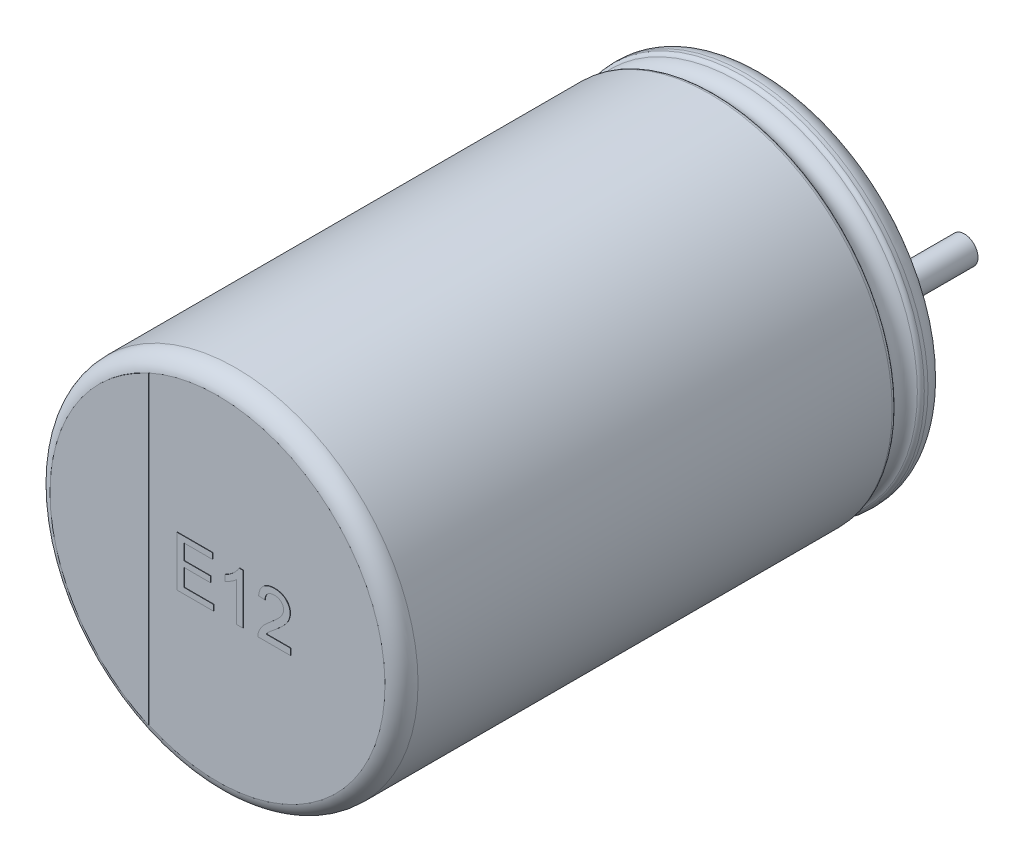
SolidWorks part; units mm, degrees
ref_plane "Plan de face" through (0, 0, 0) normal (0, 0, 1) x (1, 0, 0)
ref_plane "Plan de dessus" through (0, 0, 0) normal (0, 1, 0) x (1, 0, 0)
ref_plane "Plan de droite" through (0, 0, 0) normal (1, 0, 0) x (0, 0, -1)
sketch "Sketch10" plane through (0, 0, 0) normal (1, 0, 0) x (0, 0, -1)
  line L0 (18.1631, 0) -> (-18.9631, 0) construction
  line L1 (-12, 0) -> (-0.05, 0)
  line L2 (-12, 0) -> (-12, 3.6736)
  line L3 (-11.6, 4) -> (-1.1846, 4)
  line L4 (-0.05, 3.4031) -> (-0.05, 0)
  line L7 (-0.4794, 4) -> (-0.3982, 4)
  arc A0 (-12, 3.6736) -> (-11.6, 4) centre (-11.6068, 3.6001) cw
  arc A1 (-0.3982, 4) -> (-0.05, 3.4031) centre (-0.3982, 3.6) cw
  arc A2 (-0.5713, 3.9394) -> (-1.0926, 3.9394) centre (-0.832, 4.051) cw
  arc A3 (-1.0926, 3.9394) -> (-1.1846, 4) centre (-1.1846, 3.9) ccw
  arc A4 (-0.5713, 3.9394) -> (-0.4794, 4) centre (-0.4794, 3.9) cw
  point P4 (0.57, 0)
  point P13 (-12, 4)
  dimension "D2" = 0.4
  dimension "D3" = 0.4
  dimension "D4" = 0.1
  dimension "D5" = 0.1
  dimension "D1" = 4
revolve "Повернуть1" add sketch "Sketch10" angle 360 about L0
sketch "Эскиз2" plane through (0, 0, 0.05) normal (0, 0, -1) x (-1, 0, 0)
  line L1 (0, 0.7993) -> (0, -1.0496) construction
  line L2 (-1.75, 0) -> (3.1313, 0) construction
  circle A3 centre (-1.75, 0) radius 0.3
  circle A7 centre (1.75, 0) radius 0.3
  dimension "D1" = 3.5
extrude "Бобышка-Вытянуть1" add sketch "Эскиз2" along normal blind 2.7
sketch "Эскиз4" plane through (0, 0, 12) normal (0, 0, 1) x (1, 0, 0)
  line L0 (-1.5096, -3.3491) -> (-1.5096, 3.3491)
  circle A1 centre (0, 0) radius 3.6736 construction
  arc A2 (-1.5096, 3.3491) -> (-1.5096, -3.3491) centre (0, 0) ccw
extrude "Бобышка-Вытянуть2" add sketch "Эскиз4" along normal blind 0.01
sketch "Эскиз5" plane through (0, 0, 12) normal (0, 0, 1) x (1, 0, 0)
  text T0 "E12" font "Arial" height 1.1
extrude "Текст" add sketch "Эскиз5" along normal blind 0.01
sketch "Эскиз6" plane through (0, 0, 0.05) normal (0, 0, -1) x (-1, 0, 0)
  line L0 (-1.75, 0.4656) -> (-2.1332, 0.4656)
  line L1 (-1.75, -0.4656) -> (-2.1332, -0.4656)
  line L2 (1.75, -0.4656) -> (2.1332, -0.4656)
  line L3 (1.75, 0.4656) -> (2.1332, 0.4656)
  arc A0 (-2.3702, -0.7952) -> (2.3702, -0.7952) centre (0, 0) ccw
  arc A1 (-1.75, -0.4656) -> (-1.75, 0.4656) centre (-1.75, 0) ccw
  arc A2 (1.75, 0.4656) -> (1.75, -0.4656) centre (1.75, 0) ccw
  arc A3 (2.3702, 0.7952) -> (-2.3702, 0.7952) centre (0, 0) ccw
  arc A4 (2.1332, 0.4656) -> (2.3702, 0.7952) centre (2.1332, 0.7156) ccw
  arc A5 (2.1332, -0.4656) -> (2.3702, -0.7952) centre (2.1332, -0.7156) cw
  arc A6 (-2.3702, -0.7952) -> (-2.1332, -0.4656) centre (-2.1332, -0.7156) cw
  arc A7 (-2.1332, 0.4656) -> (-2.3702, 0.7952) centre (-2.1332, 0.7156) cw
  point P7 (2.4563, 0.4656)
  point P23 (0, -2.5)
  point P24 (0, 2.5)
  dimension "D1" = 0.25
  dimension "D2" = 5
extrude "Бобышка-Вытянуть5" add sketch "Эскиз6" along normal blind 0.05 contours A3 A7 L0 A1 L1 A6 A0 A5 L2 A2 L3 A4
